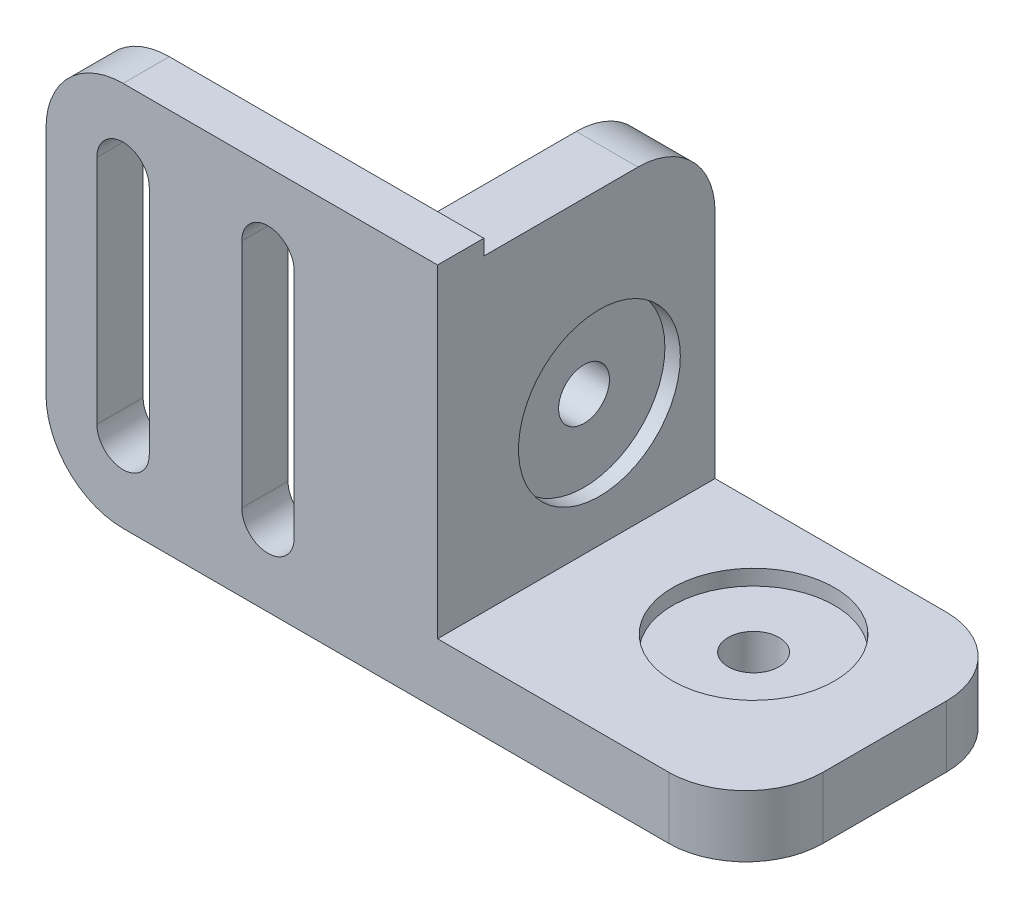
SolidWorks part; units mm, degrees
ref_plane "Plano frontal" through (0, 0, 0) normal (0, 0, 1) x (1, 0, 0)
ref_plane "Plano superior" through (0, 0, 0) normal (0, 1, 0) x (1, 0, 0)
ref_plane "Plano direito" through (0, 0, 0) normal (1, 0, 0) x (0, 0, -1)
sketch "Esboço2" plane through (0, 0, 0) normal (0, 0, 1) x (1, 0, 0)
  line L0 (0, 0) -> (20, 0)
  line L1 (20, 0) -> (20, -4)
  line L2 (20, -4) -> (-4, -4)
  line L7 (-4, -4) -> (-4, 20)
  line L8 (-4, 20) -> (0, 20)
  line L9 (0, 20) -> (0, 0)
  dimension "D1" = 20
  dimension "D3" = 4
extrude "Ressalto-extrusão2" add sketch "Esboço2" along normal blind 15
sketch "Esboço4" plane through (-4, 0, 0) normal (-1, 0, 0) x (0, 0, 1)
  line L0 (7.5, -15) -> (7.5, 20) construction
  line L2 (15, 20) -> (0, 20) construction
  line L5 (15, 20) -> (15, -4) construction
  circle A2 centre (7.5, 8) radius 1.65
  point P14 (15, 8)
  dimension "D1" = 3.3
extrude "Corte-extrusão1" cut sketch "Esboço4" against normal through all both and the other way through all
sketch "Esboço5" plane through (0, 0, 0) normal (0, 1, 0) x (1, 0, 0)
  line L0 (20, 0) -> (0, 0) construction
  line L1 (20, -15) -> (20, 0) construction
  circle A0 centre (10, -7.5) radius 1.65
  point P2 (20, -7.5)
  point P3 (10, 0)
  dimension "D1" = 3.3
extrude "Corte-extrusão2" cut sketch "Esboço5" against normal blind 15
sketch "Esboço6" plane through (0, 0, 0) normal (0, 1, 0) x (1, 0, 0)
  circle A0 centre (10, -7.5) radius 5.25
  dimension "D1" = 10.5
extrude "Corte-extrusão3" cut sketch "Esboço6" against normal blind 1
sketch "Esboço7" plane through (0, 0, 0) normal (1, 0, 0) x (0, 0, -1)
  circle A0 centre (-7.5, 8) radius 5.25
  dimension "D1" = 10.5
extrude "Corte-extrusão4" cut sketch "Esboço7" against normal blind 1
sketch "Esboço9" plane through (0, 0, 15) normal (0, 0, 1) x (1, 0, 0)
  line L0 (20, -4) -> (-25.4, -4)
  line L1 (-25.4, -4) -> (-25.4, 21)
  line L2 (-25.4, 21) -> (0, 21)
  line L3 (0, 21) -> (0, 0)
  line L6 (-20.4, 16) -> (-20.4, 1) construction
  line L7 (-11, 1) -> (-11, 16) construction
  line L8 (-22.1, 16) -> (-22.1, 1)
  line L9 (-9.3, 1) -> (-9.3, 16)
  line L10 (-18.7, 16) -> (-18.7, 1)
  line L11 (-12.7, 1) -> (-12.7, 16)
  line L12 (-4, 20) -> (-4, -4) construction
  line L13 (0, 0) -> (20, 0)
  line L14 (20, 0) -> (20, -4)
  arc A0 (-22.1, 16) -> (-18.7, 16) centre (-20.4, 16) cw
  arc A1 (-22.1, 1) -> (-18.7, 1) centre (-20.4, 1) ccw
  arc A2 (-9.3, 1) -> (-12.7, 1) centre (-11, 1) cw
  arc A3 (-9.3, 16) -> (-12.7, 16) centre (-11, 16) ccw
  dimension "D1" = 15
  dimension "D2" = 9.4
  dimension "D3" = 5
  dimension "D4" = 5
  dimension "D7" = 7
  dimension "D8" = 5
  dimension "D5" = 1.7
  dimension "D6" = 1.7
extrude "Ressalto-extrusão3" add sketch "Esboço9" along normal blind 3
fillet "Filete1" radius 5 5 edges at (-25.4, 21, 16.5) (-25.4, -4, 16.5) (20, -2, 18) (20, -2, 0) (-2, 20, 0)
equation "\"D4@Esboço9\"=\"D3@Esboço9\""
